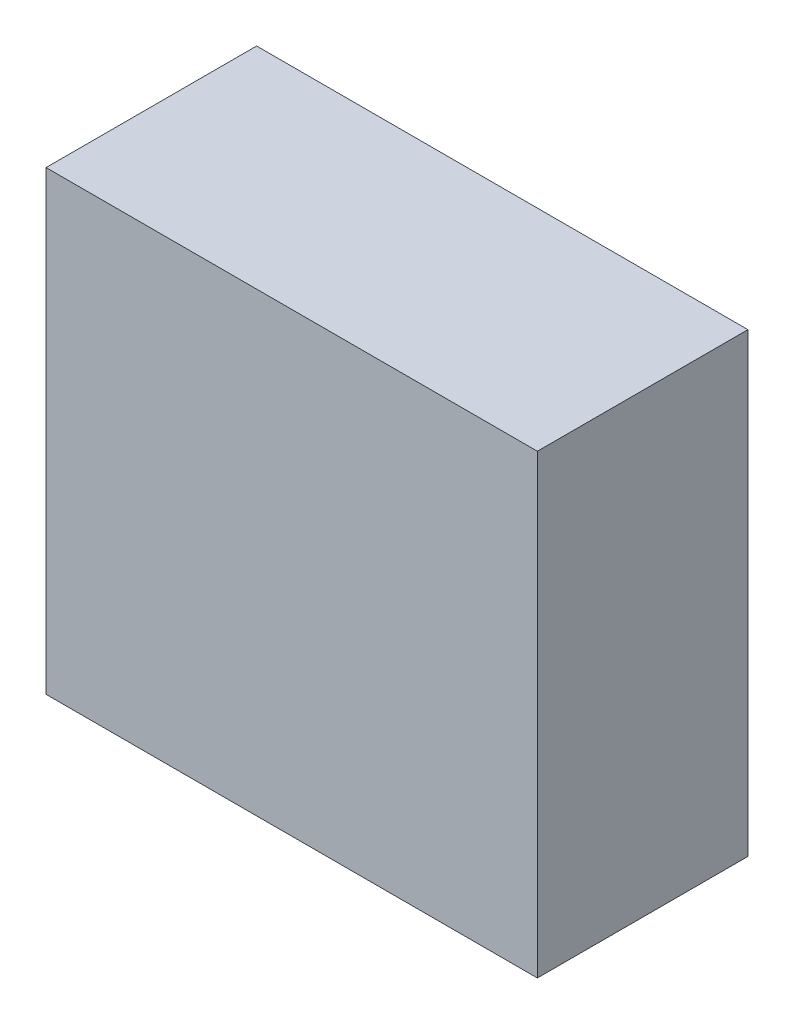
SolidWorks part; units mm, degrees
ref_plane "Front Plane" through (0, 0, 0) normal (0, 0, 1) x (1, 0, 0)
ref_plane "Top Plane" through (0, 0, 0) normal (0, 1, 0) x (1, 0, 0)
ref_plane "Right Plane" through (0, 0, 0) normal (1, 0, 0) x (0, 0, -1)
sketch "Sketch1" plane through (0, 0, 0) normal (0, 1, 0) x (1, 0, 0)
  line L1 (-88.9, -38.1) -> (88.9, -38.1)
  line L2 (-88.9, -38.1) -> (-88.9, 38.1)
  line L3 (-88.9, 38.1) -> (88.9, 38.1)
  line L4 (88.9, -38.1) -> (88.9, 38.1)
  line L5 (-88.9, -38.1) -> (88.9, 38.1) construction
  line L6 (-88.9, 38.1) -> (88.9, -38.1) construction
  point P0 (0, 0)
  dimension "D1" = 177.8
  dimension "D2" = 76.2
extrude "Boss-Extrude1" add sketch "Sketch1" along normal mid plane 165.1
